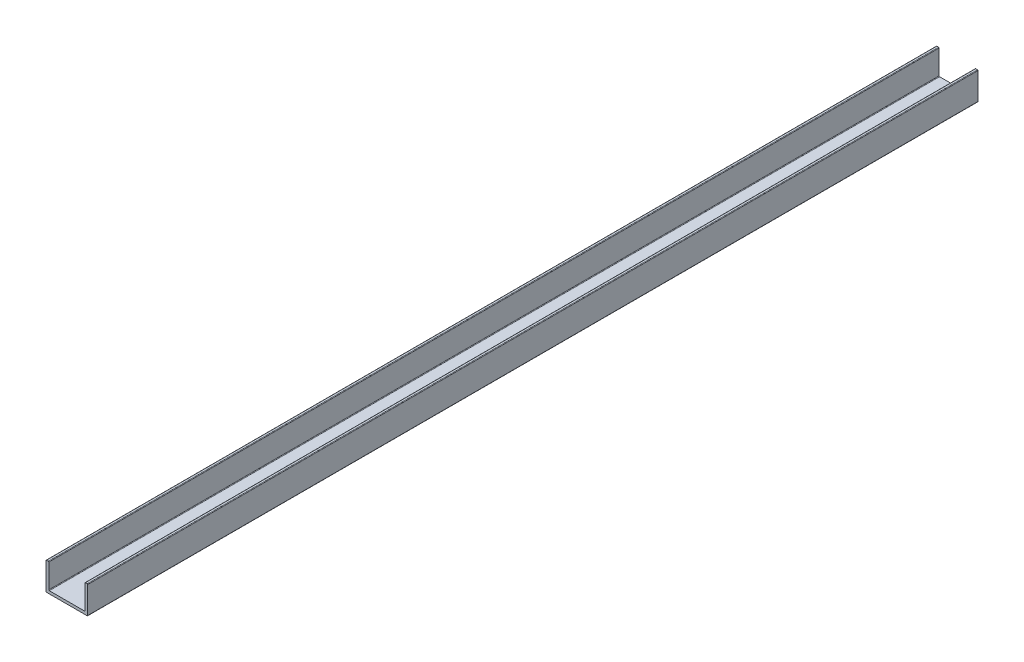
SolidWorks part; units mm, degrees
material "1060 Сплав"
ref_plane "Спереди" through (0, 0, 0) normal (0, 0, 1) x (1, 0, 0)
ref_plane "Сверху" through (0, 0, 0) normal (0, 1, 0) x (1, 0, 0)
ref_plane "Справа" through (0, 0, 0) normal (1, 0, 0) x (0, 0, -1)
sketch "П-профиль" plane through (0, 0, 0) normal (0, 0, 1) x (1, 0, 0)
  line L0 (0, 0.2) -> (0, 9.8)
  line L1 (0.2, 10) -> (0.8, 10)
  line L2 (1, 9.8) -> (1, 1.2)
  line L3 (1.2, 1) -> (13.8, 1)
  line L4 (14, 1.2) -> (14, 9.8)
  line L5 (14.2, 10) -> (14.8, 10)
  line L6 (15, 9.8) -> (15, 0.2)
  line L7 (14.8, 0) -> (0.2, 0)
  arc A0 (0, 9.8) -> (0.2, 10) centre (0.2, 9.8) cw
  arc A1 (15, 0.2) -> (14.8, 0) centre (14.8, 0.2) cw
  arc A2 (13.8, 1) -> (14, 1.2) centre (13.8, 1.2) ccw
  arc A3 (14.8, 10) -> (15, 9.8) centre (14.8, 9.8) cw
  arc A4 (14, 9.8) -> (14.2, 10) centre (14.2, 9.8) cw
  arc A5 (1, 1.2) -> (1.2, 1) centre (1.2, 1.2) ccw
  arc A6 (0, 0.2) -> (0.2, 0) centre (0.2, 0.2) ccw
  arc A7 (0.8, 10) -> (1, 9.8) centre (0.8, 9.8) cw
  point P23 (0, 0)
  point P26 (-28.9557, 18.5386)
  dimension "D5" = 0.2
  dimension "D6" = 0.2
  dimension "D1" = 10
  dimension "D2" = 15
  dimension "D3" = 1
  dimension "D4" = 1
extrude "Бобышка-Вытянуть1" add sketch "П-профиль" along normal blind 320 contours L2 A5 L3 A2 L4 A4 L5 A3 L6 A1 L7 A6 L0 A0 L1 A7
equation "\"D4@П-профиль\" = \"D3@П-профиль\""
